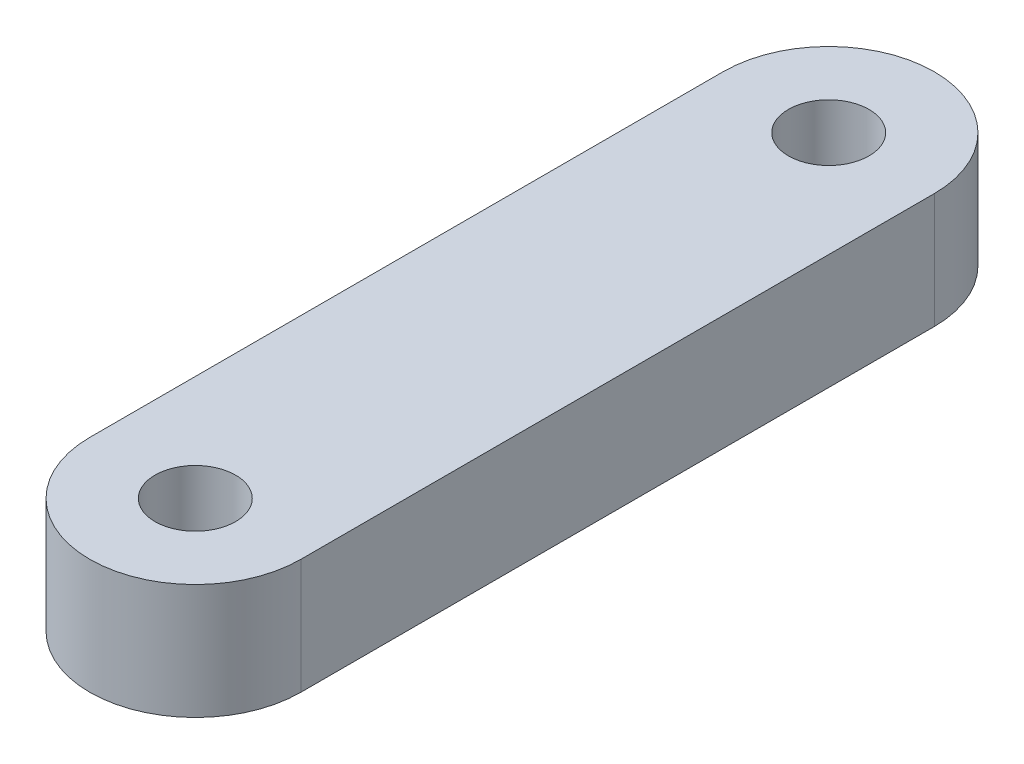
SolidWorks part; units mm, degrees
material "Acrylic (Medium-high impact)"
ref_plane "Front Plane" through (0, 0, 0) normal (0, 0, 1) x (1, 0, 0)
ref_plane "Top Plane" through (0, 0, 0) normal (0, 1, 0) x (1, 0, 0)
ref_plane "Right Plane" through (0, 0, 0) normal (1, 0, 0) x (0, 0, -1)
sketch "Sketch1" plane through (0, 0, 0) normal (0, 1, 0) x (1, 0, 0)
  line L0 (1.7536, 17.7239) -> (1.7536, -15.2761)
  line L2 (-9.2464, -15.2761) -> (-9.2464, 17.7239)
  circle A0 centre (-3.7464, -15.2761) radius 2.1
  circle A1 centre (-3.7464, 17.7239) radius 2.1
  arc A2 (-9.2464, 17.7239) -> (1.7536, 17.7239) centre (-3.7464, 17.7239) cw
  arc A3 (-9.2464, -15.2761) -> (1.7536, -15.2761) centre (-3.7464, -15.2761) ccw
  dimension "D1" = 4.2
  dimension "D3" = 4.2
  dimension "D4" = 5.5
  dimension "D6" = 4.2
  dimension "D2" = 33
  dimension "D5" = 5.5
extrude "Boss-Extrude1" add sketch "Sketch1" along normal blind 6
